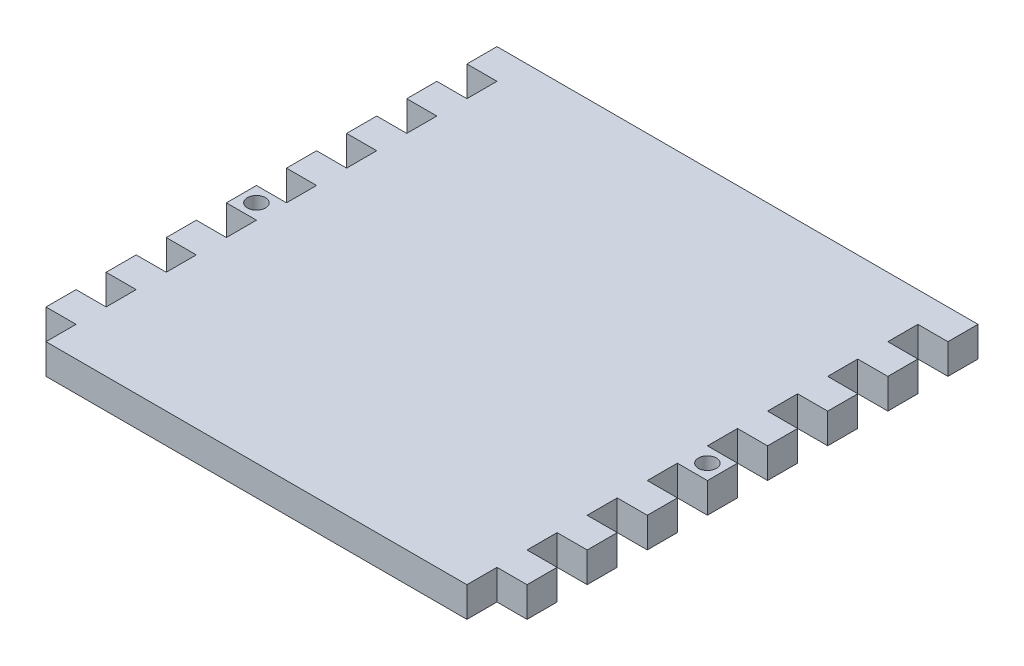
SolidWorks part; units mm, degrees
material "Balsa"
ref_plane "Plan de face" through (0, 0, 0) normal (0, 0, 1) x (1, 0, 0)
ref_plane "Plan de dessus" through (0, 0, 0) normal (0, 1, 0) x (1, 0, 0)
ref_plane "Plan de droite" through (0, 0, 0) normal (1, 0, 0) x (0, 0, -1)
sketch "Esquisse1" plane through (0, 0, 0) normal (0, 1, 0) x (1, 0, 0)
  line L1 (-35, 40) -> (35, 40)
  line L2 (-35, 40) -> (-35, -40)
  line L3 (-35, -40) -> (35, -40)
  line L4 (35, 40) -> (35, -40)
  dimension "D1" = 70
  dimension "D2" = 80
  dimension "D3" = 35
  dimension "D4" = 40
extrude "Boss.-Extru.1" add sketch "Esquisse1" along normal blind 5
sketch "Esquisse2" plane through (0, 5, 0) normal (0, 1, 0) x (1, 0, 0)
  line L1 (-35, 40) -> (-40, 40)
  line L2 (-35, 40) -> (-35, 35)
  line L3 (-35, 35) -> (-40, 35)
  line L4 (-40, 40) -> (-40, 35)
  dimension "D1" = 5
  dimension "D2" = 5
extrude "Boss.-Extru.2" add sketch "Esquisse2" against normal blind 5
pattern_linear "Répétition linéaire1" count 2 spacing 75 along (1, 0, 0) count 8 spacing 10 along (0, 0, 1) of "Boss.-Extru.2"
sketch "Esquisse3" plane through (0, 5, 0) normal (0, 1, 0) x (1, 0, 0)
  line L1 (-40, 20) -> (-40, 15) construction
  line L4 (-40, -5) -> (-35, -5) construction
  circle A0 centre (-37.5, -2.5) radius 1.5
  dimension "D1" = 3
  dimension "D2" = 2.5
  dimension "D3" = 2.5
extrude "Enlèv. mat.-Extru.1" cut sketch "Esquisse3" against normal blind 10
mirror "Symétrie1" about plane through (0, 0, 0) normal (1, 0, 0) of "Enlèv. mat.-Extru.1"
